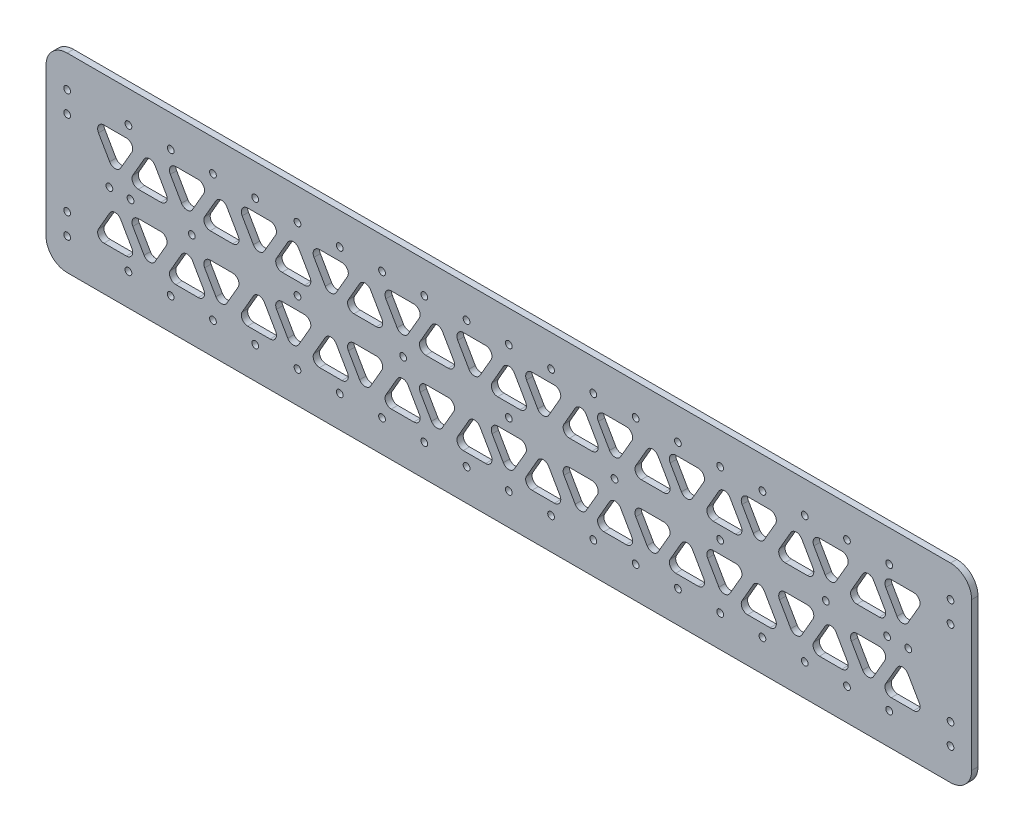
SolidWorks part; units mm, degrees
material "A-玻璃纤维"
ref_plane "前视基准面" through (0, 0, 0) normal (0, 0, 1) x (1, 0, 0)
ref_plane "上视基准面" through (0, 0, 0) normal (0, 1, 0) x (1, 0, 0)
ref_plane "右视基准面" through (0, 0, 0) normal (1, 0, 0) x (0, 0, -1)
sketch "草图1" plane through (0, 0, 0) normal (0, 0, 1) x (1, 0, 0)
  line L0 (0, 119.0633) -> (0, -125.4389) construction
  line L1 (221.2314, 0) -> (-250.8777, 0) construction
  line L3 (-219, -45) -> (219, -45)
  line L4 (-219, -45) -> (-219, 45)
  line L5 (-219, 45) -> (219, 45)
  line L6 (219, -45) -> (219, 45)
  line L7 (-219, -45) -> (219, 45) construction
  line L8 (-219, 45) -> (219, -45) construction
  circle A0 centre (0, 0) radius 1.6
  circle A1 centre (50, 0) radius 1.6
  circle A2 centre (100, 0) radius 1.6
  circle A3 centre (150, 0) radius 1.6
  circle A5 centre (-50, 0) radius 1.6
  circle A6 centre (-100, 0) radius 1.6
  circle A7 centre (-150, 0) radius 1.6
  circle A9 centre (200, 0) radius 1.6 [skipped]
  circle A10 centre (-200, 0) radius 1.6 [skipped]
  point P5 (0, 0)
  dimension "D3" = 3.2
  dimension "D6" = 50
  dimension "D7" = 50
  dimension "D1" = 438
  dimension "D2" = 90
  dimension "D4" = 5
  dimension "D5" = 5
extrude "凸台-拉伸1" add sketch "草图1" along normal blind 3
sketch "草图2" plane through (0, 0, 3) normal (0, 0, 1) x (1, 0, 0)
  line L0 (253.3129, 0) -> (-347.019, 0) construction
  line L1 (0, 205.1568) -> (0, -156.2449) construction
  line L2 (219, -45) -> (219, 45) construction
  circle A0 centre (179, 0) radius 1.6
  circle A1 centre (189, 0) radius 1.6
  circle A2 centre (-189, 0) radius 1.6
  circle A3 centre (-179, 0) radius 1.6
  circle A4 centre (209, -20) radius 1.6
  circle A5 centre (209, -30) radius 1.6
  circle A6 centre (209, 30) radius 1.6
  circle A7 centre (209, 20) radius 1.6
  circle A8 centre (-209, 20) radius 1.6
  circle A9 centre (-209, 30) radius 1.6
  circle A10 centre (-209, -30) radius 1.6
  circle A11 centre (-209, -20) radius 1.6
  dimension "D1" = 30
  dimension "D2" = 10
  dimension "D3" = 3.2
  dimension "D4" = 10
  dimension "D5" = 10
  dimension "D6" = 3.2
  dimension "D7" = 20
extrude "切除-拉伸1" cut sketch "草图2" against normal blind 10
sketch "草图3" plane through (0, 0, 3) normal (0, 0, 1) x (1, 0, 0)
  line L0 (258.6861, 0) -> (-241.2099, 0) construction
  line L1 (0, 128.791) -> (0, -119.6897) construction
  circle A0 centre (0, -30) radius 1.6
  circle A1 centre (20, -30) radius 1.6
  circle A2 centre (40, -30) radius 1.6
  circle A3 centre (60, -30) radius 1.6
  circle A4 centre (80, -30) radius 1.6
  circle A5 centre (100, -30) radius 1.6
  circle A6 centre (120, -30) radius 1.6
  circle A7 centre (140, -30) radius 1.6
  circle A8 centre (160, -30) radius 1.6
  circle A9 centre (180, -30) radius 1.6
  circle A10 centre (-20, -30) radius 1.6
  circle A11 centre (-40, -30) radius 1.6
  circle A12 centre (-60, -30) radius 1.6
  circle A13 centre (-80, -30) radius 1.6
  circle A14 centre (-100, -30) radius 1.6
  circle A15 centre (-120, -30) radius 1.6
  circle A16 centre (-140, -30) radius 1.6
  circle A17 centre (-160, -30) radius 1.6
  circle A18 centre (-180, -30) radius 1.6
  circle A19 centre (-180, 30) radius 1.6
  circle A20 centre (-160, 30) radius 1.6
  circle A21 centre (-140, 30) radius 1.6
  circle A22 centre (-120, 30) radius 1.6
  circle A23 centre (-100, 30) radius 1.6
  circle A24 centre (-80, 30) radius 1.6
  circle A25 centre (-60, 30) radius 1.6
  circle A26 centre (-40, 30) radius 1.6
  circle A27 centre (-20, 30) radius 1.6
  circle A28 centre (180, 30) radius 1.6
  circle A29 centre (160, 30) radius 1.6
  circle A30 centre (140, 30) radius 1.6
  circle A31 centre (120, 30) radius 1.6
  circle A32 centre (100, 30) radius 1.6
  circle A33 centre (80, 30) radius 1.6
  circle A34 centre (60, 30) radius 1.6
  circle A35 centre (40, 30) radius 1.6
  circle A36 centre (20, 30) radius 1.6
  circle A37 centre (0, 30) radius 1.6
  dimension "D1" = 3.2
  dimension "D2" = 30
  dimension "D5" = 20
  dimension "D6" = 20
  dimension "D3" = 10
  dimension "D4" = 10
extrude "切除-拉伸2" cut sketch "草图3" against normal blind 10
fillet "圆角1" radius 10 4 edges at (-219, 45, 1.5) (-219, -45, 1.5) (219, -45, 1.5) (219, 45, 1.5)
sketch "草图4" plane through (0, 0, 3) normal (0, 0, 1) x (1, 0, 0)
  line L0 (0, 85.9349) -> (0, -71.811) construction
  line L1 (-10.5, 6) -> (10.5, 6)
  line L2 (10.5, 6) -> (0, 24.1865)
  line L3 (0, 24.1865) -> (-10.5, 6)
  line L4 (5.7735, 24.1865) -> (16.2735, 6)
  line L5 (16.2735, 6) -> (26.7735, 24.1865)
  line L6 (26.7735, 24.1865) -> (5.7735, 24.1865)
  line L7 (-234.7552, 0) -> (342.0895, 0) construction
  line L8 (60.7735, 24.1865) -> (39.7735, 24.1865)
  line L9 (39.7735, 24.1865) -> (50.2735, 6)
  line L10 (50.2735, 6) -> (60.7735, 24.1865)
  line L11 (34, 24.1865) -> (23.5, 6)
  line L12 (23.5, 6) -> (44.5, 6)
  line L13 (44.5, 6) -> (34, 24.1865)
  line L14 (94.7735, 24.1865) -> (73.7735, 24.1865)
  line L15 (73.7735, 24.1865) -> (84.2735, 6)
  line L16 (84.2735, 6) -> (94.7735, 24.1865)
  line L17 (68, 24.1865) -> (57.5, 6)
  line L18 (57.5, 6) -> (78.5, 6)
  line L19 (78.5, 6) -> (68, 24.1865)
  line L20 (128.7735, 24.1865) -> (107.7735, 24.1865)
  line L21 (107.7735, 24.1865) -> (118.2735, 6)
  line L22 (118.2735, 6) -> (128.7735, 24.1865)
  line L23 (102, 24.1865) -> (91.5, 6)
  line L24 (91.5, 6) -> (112.5, 6)
  line L25 (112.5, 6) -> (102, 24.1865)
  line L26 (162.7735, 24.1865) -> (141.7735, 24.1865)
  line L27 (141.7735, 24.1865) -> (152.2735, 6)
  line L28 (152.2735, 6) -> (162.7735, 24.1865)
  line L29 (136, 24.1865) -> (125.5, 6)
  line L30 (125.5, 6) -> (146.5, 6)
  line L31 (146.5, 6) -> (136, 24.1865)
  line L32 (196.7735, 24.1865) -> (175.7735, 24.1865)
  line L33 (175.7735, 24.1865) -> (186.2735, 6)
  line L34 (186.2735, 6) -> (196.7735, 24.1865)
  line L35 (170, 24.1865) -> (159.5, 6)
  line L36 (159.5, 6) -> (180.5, 6)
  line L37 (180.5, 6) -> (170, 24.1865)
  line L38 (-180.5, 6) -> (-170, 24.1865)
  line L39 (-159.5, 6) -> (-180.5, 6)
  line L40 (-170, 24.1865) -> (-159.5, 6)
  line L41 (-186.2735, 6) -> (-196.7735, 24.1865)
  line L42 (-175.7735, 24.1865) -> (-186.2735, 6)
  line L43 (-196.7735, 24.1865) -> (-175.7735, 24.1865)
  line L44 (-146.5, 6) -> (-136, 24.1865)
  line L45 (-125.5, 6) -> (-146.5, 6)
  line L46 (-136, 24.1865) -> (-125.5, 6)
  line L47 (-152.2735, 6) -> (-162.7735, 24.1865)
  line L48 (-141.7735, 24.1865) -> (-152.2735, 6)
  line L49 (-162.7735, 24.1865) -> (-141.7735, 24.1865)
  line L50 (-112.5, 6) -> (-102, 24.1865)
  line L51 (-91.5, 6) -> (-112.5, 6)
  line L52 (-102, 24.1865) -> (-91.5, 6)
  line L53 (-118.2735, 6) -> (-128.7735, 24.1865)
  line L54 (-107.7735, 24.1865) -> (-118.2735, 6)
  line L55 (-128.7735, 24.1865) -> (-107.7735, 24.1865)
  line L56 (-78.5, 6) -> (-68, 24.1865)
  line L57 (-57.5, 6) -> (-78.5, 6)
  line L58 (-68, 24.1865) -> (-57.5, 6)
  line L59 (-84.2735, 6) -> (-94.7735, 24.1865)
  line L60 (-73.7735, 24.1865) -> (-84.2735, 6)
  line L61 (-94.7735, 24.1865) -> (-73.7735, 24.1865)
  line L62 (-44.5, 6) -> (-34, 24.1865)
  line L63 (-23.5, 6) -> (-44.5, 6)
  line L64 (-34, 24.1865) -> (-23.5, 6)
  line L65 (-50.2735, 6) -> (-60.7735, 24.1865)
  line L66 (-39.7735, 24.1865) -> (-50.2735, 6)
  line L67 (-60.7735, 24.1865) -> (-39.7735, 24.1865)
  line L68 (-26.7735, 24.1865) -> (-5.7735, 24.1865)
  line L69 (-16.2735, 6) -> (-26.7735, 24.1865)
  line L70 (-5.7735, 24.1865) -> (-16.2735, 6)
  line L72 (-10.5, -6) -> (0, -24.1865)
  line L73 (-5.7735, -24.1865) -> (-16.2735, -6)
  line L74 (-16.2735, -6) -> (-26.7735, -24.1865)
  line L75 (-26.7735, -24.1865) -> (-5.7735, -24.1865)
  line L76 (-60.7735, -24.1865) -> (-39.7735, -24.1865)
  line L77 (-39.7735, -24.1865) -> (-50.2735, -6)
  line L78 (-50.2735, -6) -> (-60.7735, -24.1865)
  line L79 (-34, -24.1865) -> (-23.5, -6)
  line L80 (-23.5, -6) -> (-44.5, -6)
  line L81 (-44.5, -6) -> (-34, -24.1865)
  line L82 (-94.7735, -24.1865) -> (-73.7735, -24.1865)
  line L83 (-73.7735, -24.1865) -> (-84.2735, -6)
  line L84 (-84.2735, -6) -> (-94.7735, -24.1865)
  line L85 (-68, -24.1865) -> (-57.5, -6)
  line L86 (-57.5, -6) -> (-78.5, -6)
  line L87 (-78.5, -6) -> (-68, -24.1865)
  line L88 (-128.7735, -24.1865) -> (-107.7735, -24.1865)
  line L89 (-107.7735, -24.1865) -> (-118.2735, -6)
  line L90 (-118.2735, -6) -> (-128.7735, -24.1865)
  line L91 (-102, -24.1865) -> (-91.5, -6)
  line L92 (-91.5, -6) -> (-112.5, -6)
  line L93 (-112.5, -6) -> (-102, -24.1865)
  line L94 (-162.7735, -24.1865) -> (-141.7735, -24.1865)
  line L95 (-141.7735, -24.1865) -> (-152.2735, -6)
  line L96 (-152.2735, -6) -> (-162.7735, -24.1865)
  line L97 (-136, -24.1865) -> (-125.5, -6)
  line L98 (-125.5, -6) -> (-146.5, -6)
  line L99 (-146.5, -6) -> (-136, -24.1865)
  line L100 (-196.7735, -24.1865) -> (-175.7735, -24.1865)
  line L101 (-175.7735, -24.1865) -> (-186.2735, -6)
  line L102 (-186.2735, -6) -> (-196.7735, -24.1865)
  line L103 (-170, -24.1865) -> (-159.5, -6)
  line L104 (-159.5, -6) -> (-180.5, -6)
  line L105 (-180.5, -6) -> (-170, -24.1865)
  line L106 (180.5, -6) -> (170, -24.1865)
  line L107 (159.5, -6) -> (180.5, -6)
  line L108 (170, -24.1865) -> (159.5, -6)
  line L109 (186.2735, -6) -> (196.7735, -24.1865)
  line L110 (175.7735, -24.1865) -> (186.2735, -6)
  line L111 (196.7735, -24.1865) -> (175.7735, -24.1865)
  line L112 (146.5, -6) -> (136, -24.1865)
  line L113 (125.5, -6) -> (146.5, -6)
  line L114 (136, -24.1865) -> (125.5, -6)
  line L115 (152.2735, -6) -> (162.7735, -24.1865)
  line L116 (141.7735, -24.1865) -> (152.2735, -6)
  line L117 (162.7735, -24.1865) -> (141.7735, -24.1865)
  line L118 (112.5, -6) -> (102, -24.1865)
  line L119 (91.5, -6) -> (112.5, -6)
  line L120 (102, -24.1865) -> (91.5, -6)
  line L121 (118.2735, -6) -> (128.7735, -24.1865)
  line L122 (107.7735, -24.1865) -> (118.2735, -6)
  line L123 (128.7735, -24.1865) -> (107.7735, -24.1865)
  line L124 (78.5, -6) -> (68, -24.1865)
  line L125 (57.5, -6) -> (78.5, -6)
  line L126 (68, -24.1865) -> (57.5, -6)
  line L127 (84.2735, -6) -> (94.7735, -24.1865)
  line L128 (73.7735, -24.1865) -> (84.2735, -6)
  line L129 (94.7735, -24.1865) -> (73.7735, -24.1865)
  line L130 (44.5, -6) -> (34, -24.1865)
  line L131 (23.5, -6) -> (44.5, -6)
  line L132 (34, -24.1865) -> (23.5, -6)
  line L133 (50.2735, -6) -> (60.7735, -24.1865)
  line L134 (39.7735, -24.1865) -> (50.2735, -6)
  line L135 (60.7735, -24.1865) -> (39.7735, -24.1865)
  line L136 (26.7735, -24.1865) -> (5.7735, -24.1865)
  line L137 (16.2735, -6) -> (26.7735, -24.1865)
  line L138 (5.7735, -24.1865) -> (16.2735, -6)
  line L140 (10.5, -6) -> (0, -24.1865)
  line L141 (-10.5, -6) -> (10.5, -6)
  point P6 (0, 6)
  point P75 (0, -6)
  dimension "D1" = 60
  dimension "D2" = 21
  dimension "D3" = 6
  dimension "D4" = 60
  dimension "D5" = 5
  dimension "D6" = 6
  dimension "D7" = 34
extrude "切除-拉伸3" cut sketch "草图4" against normal blind 10
fillet "圆角2" radius 3 131 edges at (26.7735, 24.1865, 1.5) (16.2735, 6, 1.5) (5.7735, 24.1865, 1.5) (152.2735, -6, 1.5) (162.7735, -24.1865, 1.5) (141.7735, -24.1865, 1.5) (146.5, -6, 1.5) (136, -24.1865, 1.5) (125.5, -6, 1.5) (118.2735, -6, 1.5) (128.7735, -24.1865, 1.5) (107.7735, -24.1865, 1.5) (112.5, -6, 1.5) (102, -24.1865, 1.5) (91.5, -6, 1.5) (180.5, -6, 1.5) (170, -24.1865, 1.5) (159.5, -6, 1.5) (186.2735, -6, 1.5) (196.7735, -24.1865, 1.5) (175.7735, -24.1865, 1.5) (-186.2735, -6, 1.5) (-175.7735, -24.1865, 1.5) (-196.7735, -24.1865, 1.5) (-180.5, -6, 1.5) (-159.5, -6, 1.5) (26.7735, -24.1865, 1.5) (5.7735, -24.1865, 1.5) (16.2735, -6, 1.5) (84.2735, -6, 1.5) (94.7735, -24.1865, 1.5) (73.7735, -24.1865, 1.5) (78.5, -6, 1.5) (68, -24.1865, 1.5) (57.5, -6, 1.5) (50.2735, -6, 1.5) (60.7735, -24.1865, 1.5) (39.7735, -24.1865, 1.5) (44.5, -6, 1.5) (34, -24.1865, 1.5) (23.5, -6, 1.5) (-186.2735, 6, 1.5) (-175.7735, 24.1865, 1.5) (-146.5, 6, 1.5) (-136, 24.1865, 1.5) (-152.2735, 6, 1.5) (-162.7735, 24.1865, 1.5) (-112.5, 6, 1.5) (-102, 24.1865, 1.5) (-91.5, 6, 1.5) (146.5, 6, 1.5) (125.5, 6, 1.5) (136, 24.1865, 1.5) (152.2735, 6, 1.5) (141.7735, 24.1865, 1.5) (162.7735, 24.1865, 1.5) (180.5, 6, 1.5) (159.5, 6, 1.5) (170, 24.1865, 1.5) (186.2735, 6, 1.5) (175.7735, 24.1865, 1.5) (196.7735, 24.1865, 1.5) (10.5, 6, 1.5) (-10.5, 6, 1.5) (0, 24.1865, 1.5) (-180.5, 6, 1.5) (-170, 24.1865, 1.5) (-159.5, 6, 1.5) (44.5, 6, 1.5) (34, 24.1865, 1.5) (50.2735, 6, 1.5) (39.7735, 24.1865, 1.5) (60.7735, 24.1865, 1.5) (118.2735, 6, 1.5) (107.7735, 24.1865, 1.5) (128.7735, 24.1865, 1.5) (112.5, 6, 1.5) (91.5, 6, 1.5) (102, 24.1865, 1.5) (84.2735, 6, 1.5) (73.7735, 24.1865, 1.5) (94.7735, 24.1865, 1.5) (78.5, 6, 1.5) (57.5, 6, 1.5) (68, 24.1865, 1.5) (-84.2735, -6, 1.5) (-73.7735, -24.1865, 1.5) (-94.7735, -24.1865, 1.5) (-78.5, -6, 1.5) (-57.5, -6, 1.5) (-68, -24.1865, 1.5) (-50.2735, -6, 1.5) (-39.7735, -24.1865, 1.5) (-60.7735, -24.1865, 1.5) (-44.5, -6, 1.5) (-34, -24.1865, 1.5) (-152.2735, -6, 1.5) (-141.7735, -24.1865, 1.5) (-162.7735, -24.1865, 1.5) (-146.5, -6, 1.5) (-125.5, -6, 1.5) (-136, -24.1865, 1.5) (-118.2735, -6, 1.5) (-128.7735, -24.1865, 1.5) (-112.5, -6, 1.5) (-91.5, -6, 1.5) (-102, -24.1865, 1.5) (-44.5, 6, 1.5) (-34, 24.1865, 1.5) (-23.5, 6, 1.5) (-84.2735, 6, 1.5) (-94.7735, 24.1865, 1.5) (-73.7735, 24.1865, 1.5) (-78.5, 6, 1.5) (-68, 24.1865, 1.5) (-57.5, 6, 1.5) (-118.2735, 6, 1.5) (-128.7735, 24.1865, 1.5) (-107.7735, 24.1865, 1.5) (-50.2735, 6, 1.5) (-60.7735, 24.1865, 1.5) (-39.7735, 24.1865, 1.5) (-26.7735, 24.1865, 1.5) (-5.7735, 24.1865, 1.5) (-16.2735, 6, 1.5) (-26.7735, -24.1865, 1.5) (-16.2735, -6, 1.5) (-5.7735, -24.1865, 1.5) (10.5, -6, 1.5) (-10.5, -6, 1.5) (-196.7735, 24.1865, 1.5)
